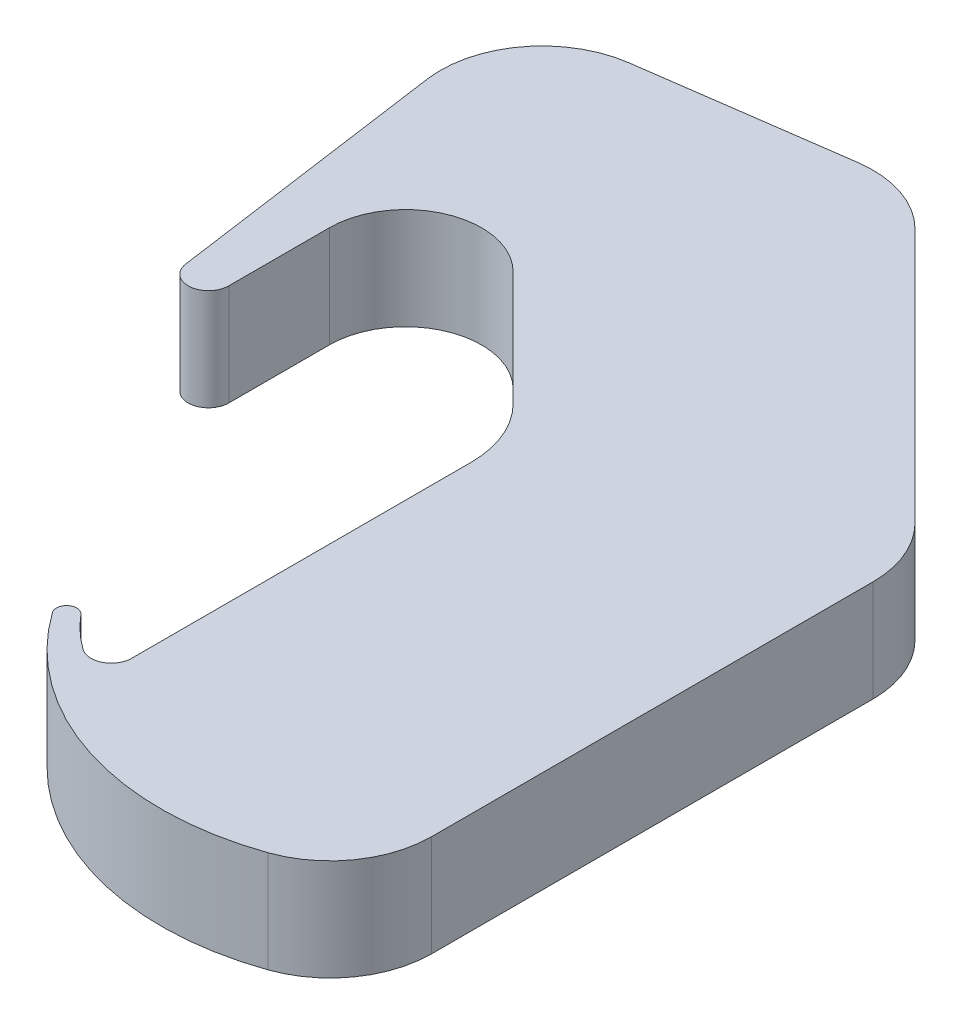
SolidWorks part; units mm, degrees
ref_plane "Alzado" through (0, 0, 0) normal (0, 0, 1) x (1, 0, 0)
ref_plane "Planta" through (0, 0, 0) normal (0, 1, 0) x (1, 0, 0)
ref_plane "Vista lateral" through (0, 0, 0) normal (1, 0, 0) x (0, 0, -1)
sketch "Croquis1" plane through (0, 0, 0) normal (0, 1, 0) x (1, 0, 0)
  line L0 (-72.4359, -12.1396) -> (-54.8685, -12.1396) construction
  line L1 (-55.5959, 49.0835) -> (-25.5959, 49.0835)
  line L2 (-55.5959, 49.0835) -> (-55.5959, -20.1396)
  line L3 (-55.5959, -20.1396) -> (-25.5959, -20.1396)
  line L4 (-25.5959, 49.0835) -> (-25.5959, -20.1396)
  line L5 (-25.5959, 33.4584) -> (-57.1891, 65.0516)
  line L6 (-57.1891, 65.0516) -> (-91.8504, 60.1941)
  line L7 (-91.8504, 60.1941) -> (-86.299, 20.5812)
  line L8 (-86.299, 20.5812) -> (-82.5959, 21.1002)
  line L9 (-82.5959, 21.1002) -> (-82.5959, 32.7538)
  line L10 (-114.9066, 34.748) -> (-11.0104, 49.3081) construction
  line L11 (-69.7926, 38.0571) -> (-55.5959, 23.8604)
  line L12 (-61.5959, 6.8056) -> (-61.5959, -3.64) construction
  line L13 (-62.5959, -25.1396) -> (-17.3321, -25.1396) construction
  circle A0 centre (-75.0959, 32.7538) radius 7.5
  circle A1 centre (-84.5959, 22.8394) radius 2
  circle A3 centre (-41.2906, 1.9929) radius 27.1325
  circle A4 centre (-62.5959, -13.1396) radius 1
  circle A5 centre (-49.1559, -1.9859) radius 16.4654
  point P24 (0, 0)
  point P27 (-57.1891, 0)
  point P32 (-55.5959, -17.1396)
  dimension "D3" = 15
  dimension "D11" = 4
  dimension "D13" = 2
  dimension "D1" = 30
  dimension "D2" = 44
  dimension "D4" = 35
  dimension "D5" = 40
  dimension "D6" = 27
  dimension "D7" = 25.5959
  dimension "D8" = 45
  dimension "D9" = 22
  dimension "28" = 28
  dimension "D10" = 20.1396
  dimension "D12" = 6
  dimension "D14" = 8
  dimension "D15" = 5
  dimension "D16" = 3
extrude "Saliente-Extruir1" add sketch "Croquis1" along normal blind 10 contours L2 A5 | A5 L2 L3 L4 A3 | A3 L4 L5 L1 L2 | A3 L2 L1 L5 L6 L7 A1 L9 A0 L11 | A1 | A5 A4 A3 L3 L2 | A4 | L2 A3 L11
fillet "Redondeo1" radius 10 5 edges at (-91.8504, 5, -60.1941) (-25.5959, 5, 20.1396) (-57.1891, 5, -65.0516) (-25.5959, 5, -33.4584) (-55.5959, 5, -23.8604)
fillet "Redondeo2" radius 2 1 edges at (-55.5959, 5, 17.1396)
